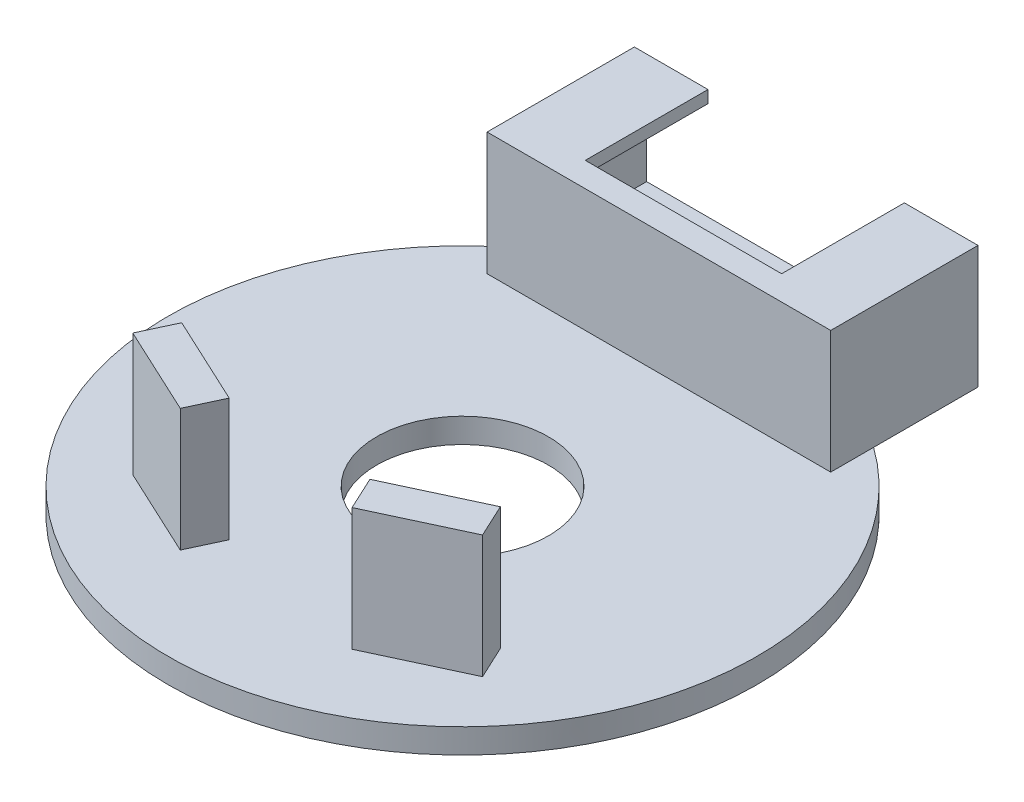
SolidWorks part; units mm, degrees
ref_plane "Plano frontal" through (0, 0, 0) normal (0, 0, 1) x (1, 0, 0)
ref_plane "Plano superior" through (0, 0, 0) normal (0, 1, 0) x (1, 0, 0)
ref_plane "Plano direito" through (0, 0, 0) normal (1, 0, 0) x (0, 0, -1)
sketch "Sketch1" plane through (0, 0, 0) normal (0, 1, 0) x (1, 0, 0)
  circle A0 centre (0, 0) radius 12
  circle A1 centre (0, 0) radius 3.5
  dimension "D1" = 24
  dimension "D2" = 7
extrude "Boss-Extrude1" add sketch "Sketch1" along normal mid plane 1
sketch "Sketch2" plane through (0, 0.5, 0) normal (0, 1, 0) x (1, 0, 0)
  line L1 (-7, 14) -> (7, 14)
  line L2 (-7, 14) -> (-7, 8)
  line L3 (-7, 8) -> (7, 8)
  line L4 (7, 14) -> (7, 8)
  circle A0 centre (0, 0) radius 12 construction
  point P4 (0, 8)
  dimension "D3" = 2
  dimension "D1" = 6
  dimension "D2" = 14
extrude "Boss-Extrude2" add sketch "Sketch2" along normal blind 5
sketch "Sketch3" plane through (0, 0, -14) normal (0, 0, -1) x (-1, 0, 0)
  line L0 (-7, 0.5) -> (7, 0.5) construction
  line L1 (-6.5, 5) -> (6.5, 5)
  line L2 (-6.5, 5) -> (-6.5, 1)
  line L3 (-6.5, 1) -> (6.5, 1)
  line L4 (6.5, 5) -> (6.5, 1)
  line L5 (-7, 5.5) -> (-7, 0.5) construction
  point P8 (0, 1)
  point P10 (-7, 3)
  point P11 (-6.5, 3)
extrude "Cut-Extrude1" cut sketch "Sketch3" against normal offset from surface (5 mm away) 1 up to face at (0, 3, -8)
sketch "Sketch4" plane through (0, 5.5, 0) normal (0, 1, 0) x (1, 0, 0)
  line L0 (7, 14) -> (-7, 14) construction
  line L1 (-4, 14) -> (4, 14)
  line L2 (-4, 14) -> (-4, 9)
  line L3 (-4, 9) -> (4, 9)
  line L4 (4, 14) -> (4, 9)
  line L5 (-7, 14) -> (-7, 8) construction
  line L6 (-7, 8) -> (7, 8) construction
  point P12 (0, 8)
  point P13 (0, 9)
  dimension "D1" = 3
  dimension "D2" = 1
extrude "Cut-Extrude2" cut sketch "Sketch4" against normal up to surface (4.5 mm away) up to face at (0, 1, -11.5)
sketch "Sketch5" plane through (0, 0.5, 0) normal (0, 1, 0) x (1, 0, 0)
  line L0 (-8.9443, -8) -> (8.9443, -8) construction
  line L1 (-6.4913, -4.9501) -> (-2.8661, -6.6405)
  line L2 (-2.8661, -6.6405) -> (-3.5, -8)
  line L3 (-3.5, -8) -> (-7.1252, -6.3095)
  line L4 (-7.1252, -6.3095) -> (-6.4913, -4.9501)
  line L5 (0, -3.3) -> (0, 3.3) construction
  line L6 (7.1252, -6.3095) -> (6.4913, -4.9501)
  line L7 (3.5, -8) -> (7.1252, -6.3095)
  line L8 (2.8661, -6.6405) -> (3.5, -8)
  line L9 (6.4913, -4.9501) -> (2.8661, -6.6405)
  arc A0 (-7, 9.7468) -> (7, 9.7468) centre (0, 0) ccw construction
  dimension "D1" = 4
  dimension "D2" = 4
  dimension "D3" = 1.5
  dimension "D4" = 7
  dimension "D5" = 25
extrude "Boss-Extrude3" add sketch "Sketch5" along normal up to surface (5 mm away) up to face at (0, 5.5, -11.25)
